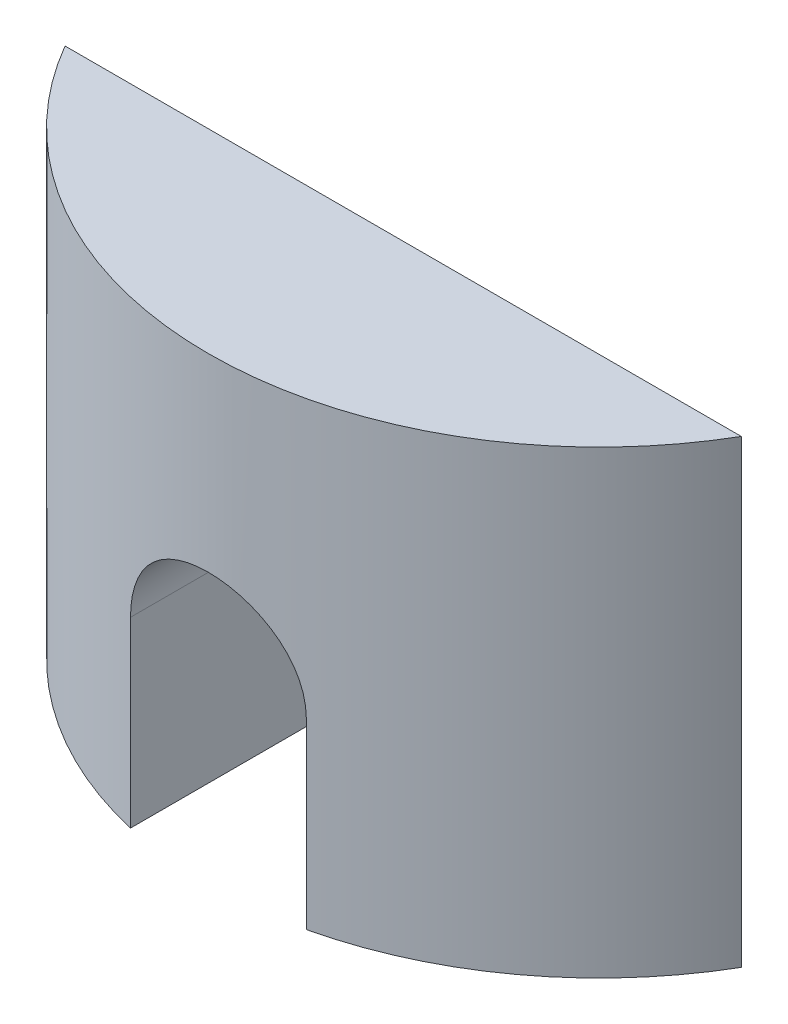
SolidWorks part; units mm, degrees
ref_plane "Front Plane" through (0, 0, 0) normal (0, 0, 1) x (1, 0, 0)
ref_plane "Top Plane" through (0, 0, 0) normal (0, 1, 0) x (1, 0, 0)
ref_plane "Right Plane" through (0, 0, 0) normal (1, 0, 0) x (0, 0, -1)
sketch "Sketch2" plane through (0, 0, 0) normal (0, 1, 0) x (1, 0, 0)
  line L0 (0, 0) -> (25, 0)
  arc A0 (0, 0) -> (25, 0) centre (12.5, 7.2507) ccw
  point P5 (12.5, -7.2)
  dimension "D2" = 25
  dimension "D1" = 7.2
extrude "Boss-Extrude1" add sketch "Sketch2" along normal blind 17
sketch "Sketch3" plane through (0, 0, 0) normal (0, 0, -1) x (-1, 0, 0)
  line L0 (-15.75, 0) -> (-15.75, 6.75)
  line L1 (-25, 0) -> (0, 0) construction
  line L2 (-15.75, 0) -> (-9.25, 0)
  line L3 (-9.25, 6.75) -> (-9.25, 0)
  arc A0 (-9.25, 6.75) -> (-15.75, 6.75) centre (-12.5, 6.75) ccw
  point P7 (-12.5, 0)
  point P8 (-12.5, 10)
  dimension "D2" = 10
  dimension "D1" = 6.5
extrude "Cut-Extrude1" cut sketch "Sketch3" against normal up to next
